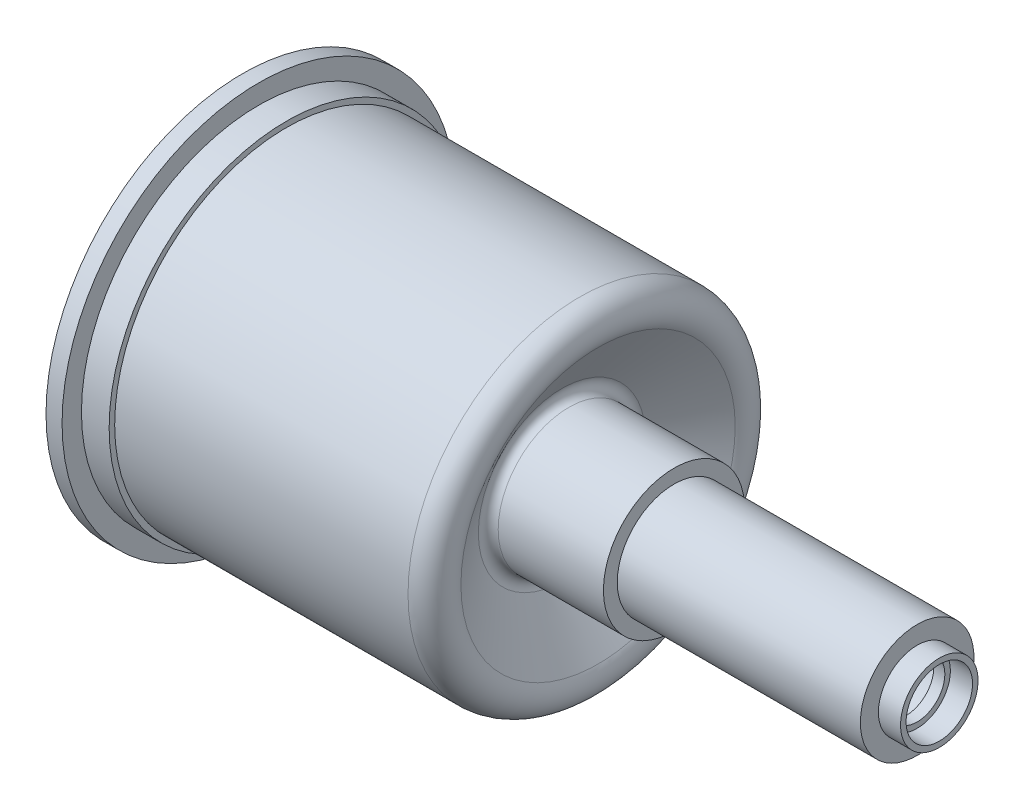
SolidWorks part; units mm, degrees
material "PE Low/Medium Density"
ref_plane "Front Plane" through (0, 0, 0) normal (0, 0, 1) x (1, 0, 0)
ref_plane "Top Plane" through (0, 0, 0) normal (0, 1, 0) x (1, 0, 0)
ref_plane "Right Plane" through (0, 0, 0) normal (1, 0, 0) x (0, 0, -1)
sketch "Sketch1" plane through (0, 0, 0) normal (0, 0, 1) x (1, 0, 0)
  line L3 (0, 15.748) -> (29.4478, 15.748)
  line L6 (38.1, 6.477) -> (38.1, 5.207)
  line L7 (38.1, 5.207) -> (60.4012, 5.207)
  line L8 (60.4012, 5.207) -> (60.4012, 3.556)
  line L9 (60.4012, 3.556) -> (62.4332, 3.556)
  line L10 (62.4332, 3.556) -> (62.4332, 0)
  line L11 (62.4332, 0) -> (0, 0)
  line L12 (-43.926, 0) -> (155.1585, 0) construction
  line L13 (0, 15.748) -> (0, 0)
  line L14 (31.1322, 12.5794) -> (27.8163, 7.6652)
  line L15 (28.448, 6.477) -> (38.1, 6.477)
  arc A2 (29.4478, 15.748) -> (31.1322, 12.5794) centre (29.4478, 13.716) cw
  arc A3 (27.8163, 7.6652) -> (28.448, 6.477) centre (28.448, 7.239) ccw
  point P10 (31.242, 14.6698)
  point P13 (0, 0)
  dimension "D8" = 31.496
  dimension "D10" = 0.762
  dimension "D11" = 38.1
  dimension "D5" = 2.032
  dimension "D1" = 31.242
  dimension "D2" = 12.954
  dimension "D3" = 9.652
  dimension "D4" = 22.3012
  dimension "D6" = 10.414
  dimension "D7" = 2.032
  dimension "D9" = 7.112
revolve "Revolve1" add sketch "Sketch1" angle 360 about L12
shell "Shell2" thickness 1.016
sketch "Sketch2" plane through (62.4332, 0, 0) normal (1, 0, 0) x (0, 0, -1)
  circle A2 centre (0, 0) radius 3.048
  circle A3 centre (0, 0) radius 3.048
  dimension "D1" = 0.508
extrude "Cut-Extrude1" cut sketch "Sketch2" against normal blind 2.032
sketch "Sketch3" plane through (0, 0, 0) normal (0, 0, 1) x (1, 0, 0)
  line L0 (0, 15.748) -> (0, -15.748) construction
  line L1 (-1.4732, 18.034) -> (0, 18.034)
  line L2 (-1.4732, 18.034) -> (-1.4732, 14.224)
  line L3 (-1.4732, 14.224) -> (0, 14.224)
  line L4 (0, 18.034) -> (0, 14.224)
  line L5 (-1.4732, 18.034) -> (0, 14.224) construction
  line L6 (-1.4732, 14.224) -> (0, 18.034) construction
  line L7 (-13.4705, 0) -> (63.5304, 0) construction
  line L8 (29.4478, 15.748) -> (0, 15.748) construction
  point P4 (-0.7366, 16.129)
  point P10 (-0.7366, 14.224)
  dimension "D1" = 1.524
  dimension "D2" = 3.81
  dimension "D3" = 1.4732
revolve "Revolve2" add sketch "Sketch3" angle 360 about L7
sketch "Sketch4" plane through (0, 0, 0) normal (0, 0, 1) x (1, 0, 0)
sketch "Sketch5" plane through (0, 0, 0) normal (0, 0, 1) x (1, 0, 0)
  line L0 (-12.0754, 0) -> (101.6304, 0) construction
  line L1 (0, 15.748) -> (2.54, 15.748)
  line L2 (0, 15.748) -> (0, 16.256)
  line L3 (0, 16.256) -> (2.54, 16.256)
  line L4 (2.54, 15.748) -> (2.54, 16.256)
  line L5 (0, 15.748) -> (2.54, 16.256) construction
  line L6 (0, 16.256) -> (2.54, 15.748) construction
  point P4 (1.27, 16.002)
  dimension "D1" = 2.54
  dimension "D2" = 0.508
revolve "Revolve4" add sketch "Sketch5" angle 360 about L0
